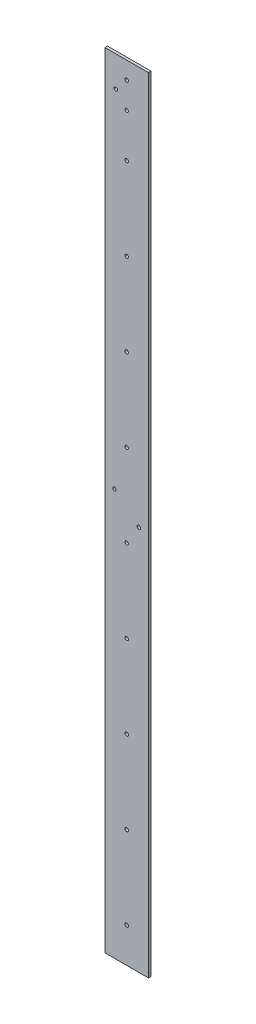
SolidWorks part; units mm, degrees
ref_plane "Front Plane" through (0, 0, 0) normal (0, 0, 1) x (1, 0, 0)
ref_plane "Top Plane" through (0, 0, 0) normal (0, 1, 0) x (1, 0, 0)
ref_plane "Right Plane" through (0, 0, 0) normal (1, 0, 0) x (0, 0, -1)
sketch "Sketch2" plane through (0, 0, 0) normal (0, 0, 1) x (1, 0, 0)
  line L0 (-24.628, -449.721) -> (25.372, -449.721)
  line L1 (25.372, -449.721) -> (25.372, 450.279)
  line L2 (25.372, 450.279) -> (-24.628, 450.279)
  line L3 (-24.628, 450.279) -> (-24.628, -449.721)
  dimension "D1" = 900
extrude "Boss-Extrude1" add sketch "Sketch2" along normal blind 3
sketch "Sketch3" plane through (0, 0, 3) normal (0, 0, 1) x (1, 0, 0)
  line L0 (0.372, 450.279) -> (0.372, -449.721) construction
  line L1 (25.372, 450.279) -> (-24.628, 450.279) construction
  line L2 (-24.628, -449.721) -> (25.372, -449.721) construction
  circle A0 centre (0.372, 350.279) radius 2
  circle A1 centre (0.372, 400.279) radius 2
  circle A2 centre (0.372, 400.279) radius 2
  circle A3 centre (0.372, 430.279) radius 2
  circle A4 centre (0.372, 430.279) radius 2
  circle A5 centre (-12.128, 415.279) radius 2
  circle A6 centre (-12.128, 415.279) radius 2
  circle A7 centre (0.372, 255.279) radius 2
  circle A8 centre (0.372, 160.279) radius 2
  circle A9 centre (0.372, 65.279) radius 2
  circle A10 centre (0.372, -29.721) radius 2
  circle A11 centre (0.372, -124.721) radius 2
  circle A12 centre (0.372, -219.721) radius 2
  circle A13 centre (0.372, -314.721) radius 2
  circle A14 centre (0.372, -409.721) radius 2
  circle A15 centre (14.372, -7.2009) radius 2
  circle A16 centre (-13.628, 16.9275) radius 2
  dimension "D4" = 4
  dimension "D5" = 50
  dimension "D7" = 14
  dimension "D8" = 14
  dimension "D1" = 0
  dimension "D2" = 0
  dimension "D3" = 0
  dimension "D6" = 9
extrude "Cut-Extrude1" cut sketch "Sketch3" against normal up to next
